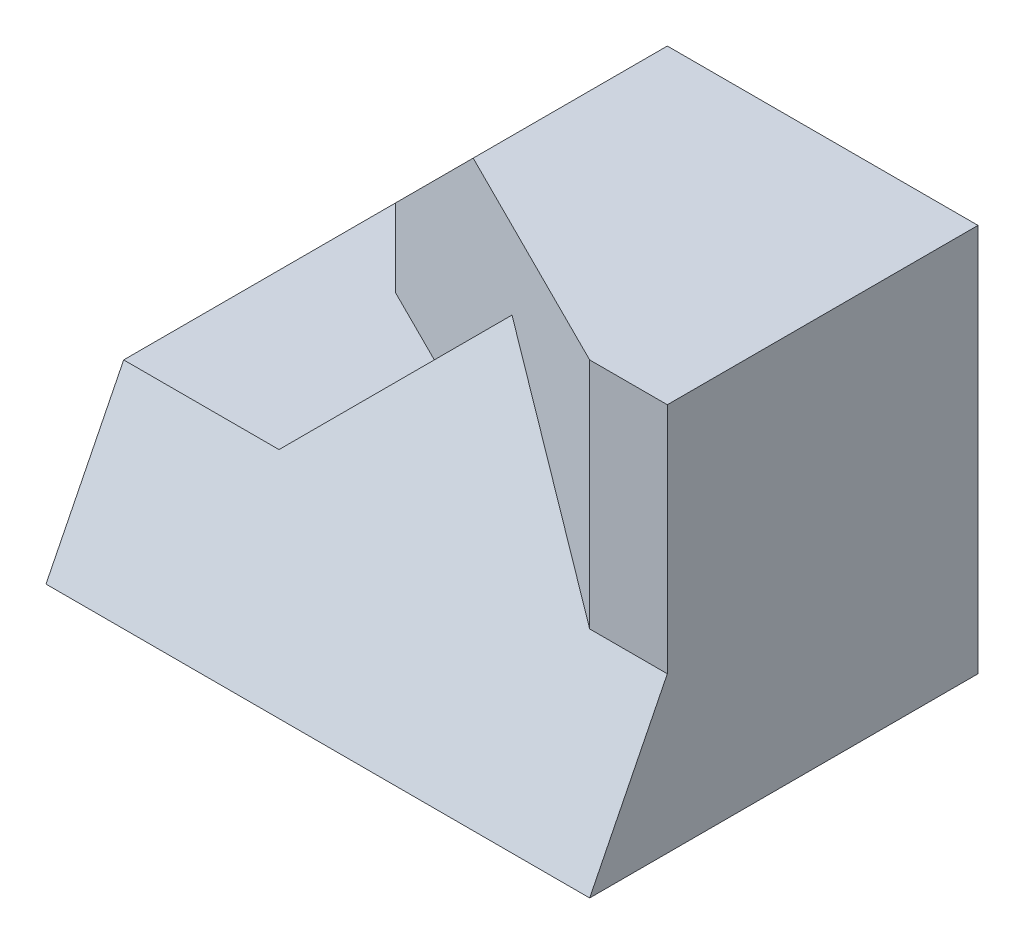
SolidWorks part; units mm, degrees
ref_plane "Front" through (0, 0, 0) normal (0, 0, 1) x (1, 0, 0)
ref_plane "Top" through (0, 0, 0) normal (0, 1, 0) x (1, 0, 0)
ref_plane "Right" through (0, 0, 0) normal (1, 0, 0) x (0, 0, -1)
sketch "Sketch1" plane through (0, 0, 0) normal (0, 0, 1) x (1, 0, 0)
  line L0 (-3, 0.5) -> (-1, 2.5)
  line L1 (-3, -2.5) -> (3, -2.5)
  line L2 (-3, -2.5) -> (-3, 0.5)
  line L3 (-1, 2.5) -> (3, 2.5)
  line L4 (3, -2.5) -> (3, 2.5)
  line L5 (-3, -2.5) -> (3, 2.5) construction
  line L6 (-3, 2.5) -> (3, -2.5) construction
  point P0 (0, 0)
  dimension "D1" = 5
  dimension "D2" = 6
extrude "Boss-Extrude1" add sketch "Sketch1" along normal blind 4
sketch "Sketch2" plane through (0, -2.5, 0) normal (0, -1, 0) x (1, 0, 0)
  line L1 (3, 0) -> (-4, 0)
  line L2 (3, 0) -> (3, 5)
  line L3 (3, 5) -> (-4, 5)
  line L4 (-4, 0) -> (-4, 5)
  dimension "D1" = 7
  dimension "D2" = 5
extrude "Boss-Extrude2" add sketch "Sketch2" against normal blind 2
sketch "Sketch3" plane through (0, 2.5, 0) normal (0, 1, 0) x (1, 0, 0)
  line L0 (2, -4) -> (-3, -1.5)
  line L1 (3, -4) -> (-1, -4) construction
  line L2 (-3, -4) -> (-3, 0) construction
  line L3 (2, -4) -> (-3, -4)
  line L4 (-3, -4) -> (-3, -1.5)
  dimension "D1" = 1
  dimension "D2" = 1.5
extrude "Cut-Extrude1" cut sketch "Sketch3" against normal blind 3
sketch "Sketch4" plane through (0, 0, 0) normal (0, 0, -1) x (-1, 0, 0)
  line L0 (-2, -0.5) -> (0, 1.5)
  line L1 (0, 1.5) -> (2, -0.5)
  line L2 (-2, -0.5) -> (3, -0.5) construction
  line L3 (2, -0.5) -> (4, -0.5)
  line L4 (4, -0.5) -> (4, -2.5)
  line L5 (4, -2.5) -> (-3, -2.5)
  line L6 (-3, -2.5) -> (-3, -0.5)
  line L7 (-3, -0.5) -> (-2, -0.5)
  dimension "D1" = 2
  dimension "D2" = 2
  dimension "D3" = 2
extrude "Boss-Extrude3" add sketch "Sketch4" against normal blind 5
sketch "Sketch5" plane through (-4, 0, 0) normal (-1, 0, 0) x (0, 0, 1)
  line L0 (5, -2.5) -> (4, -0.5)
  line L1 (4, -0.5) -> (5, -0.5)
  line L2 (5, -0.5) -> (5, -2.5)
extrude "Cut-Extrude2" cut sketch "Sketch5" against normal blind 15
sketch3d "3DSketch3"
  line L0 (-2, -0.5, 4) -> (0, 1.5, 3)
  line L1 (0, 1.5, 5) -> (0, 1.5, 3) construction
  line L2 (0, 1.5, 3) -> (2, -0.5, 4)
  line L3 (2, -0.5, 4) -> (-2, -0.5, 4)
  dimension "D1" = 0
extrude "Cut-Extrude3" cut sketch "3DSketch3" along direction (0, 0, 1) on the side of the normal blind 15
